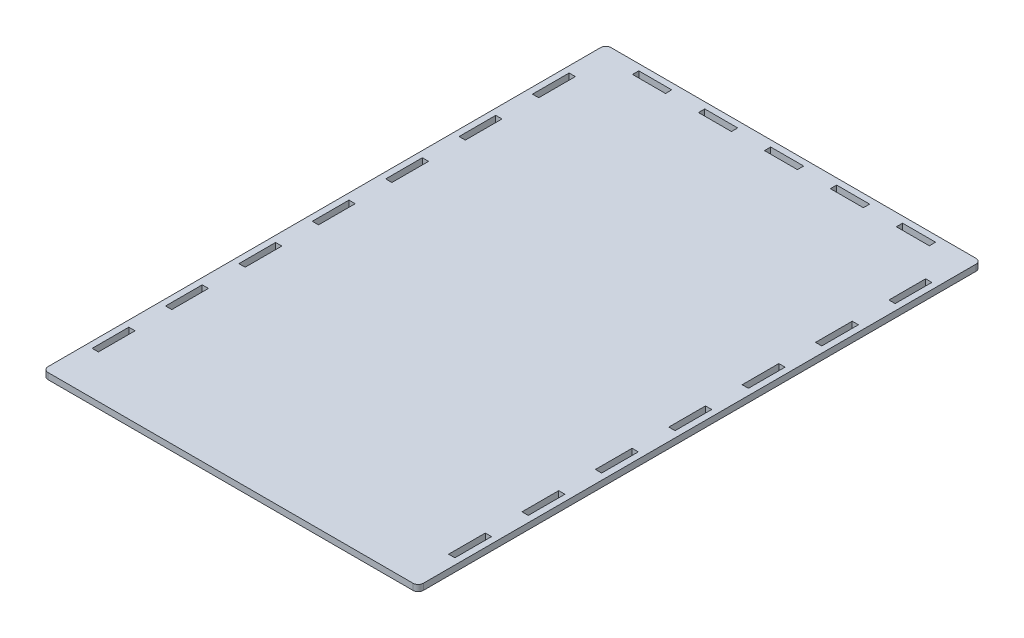
SolidWorks part; units mm, degrees
ref_plane "Front Plane" through (0, 0, 0) normal (0, 0, 1) x (1, 0, 0)
ref_plane "Top Plane" through (0, 0, 0) normal (0, 1, 0) x (1, 0, 0)
ref_plane "Right Plane" through (0, 0, 0) normal (1, 0, 0) x (0, 0, -1)
sketch "Sketch1" plane through (0, 0, 0) normal (0, 1, 0) x (1, 0, 0)
  line L3 (90, 135) -> (90, -135)
  line L6 (90, -135) -> (-90, -135)
  line L9 (-90, -135) -> (-90, 135)
  line L14 (-90, 135) -> (90, 135)
  line L15 (0, 135) -> (0, -135) construction
  point P1 (0, 0)
  point P4 (0, 135)
  point P21 (0, -135)
  dimension "D1" = 180
  dimension "D3" = 270
extrude "Boss-Extrude1" add sketch "Sketch1" along normal blind 3
sketch "Sketch2" plane through (0, 3, 0) normal (0, 1, 0) x (1, 0, 0)
  line L0 (-55.3636, 129) -> (-39.5455, 129) construction
  line L1 (-7.9091, 129) -> (7.9091, 129)
  line L2 (-7.9091, 129) -> (-7.9091, 132)
  line L3 (-7.9091, 132) -> (7.9091, 132)
  line L4 (7.9091, 129) -> (7.9091, 132)
  line L5 (-7.9091, 129) -> (7.9091, 132) construction
  line L6 (-7.9091, 132) -> (7.9091, 129) construction
  line L7 (23.7273, 129) -> (39.5455, 129)
  line L8 (23.7273, 129) -> (23.7273, 132)
  line L9 (23.7273, 132) -> (39.5455, 132)
  line L10 (39.5455, 129) -> (39.5455, 132)
  line L11 (23.7273, 129) -> (39.5455, 132) construction
  line L12 (23.7273, 132) -> (39.5455, 129) construction
  line L13 (55.3636, 129) -> (71.1818, 129)
  line L14 (55.3636, 129) -> (55.3636, 132)
  line L15 (55.3636, 132) -> (71.1818, 132)
  line L16 (87, 132) -> (-87, 132)
  line L17 (-87, 132) -> (-87, -132)
  line L18 (-90, 135) -> (-90, -135) construction
  line L19 (84, -79.2) -> (84, -96.8) construction
  line L20 (-87, -132) -> (87, -132)
  line L21 (87, -79.2) -> (84, -79.2)
  line L22 (87, -79.2) -> (87, -61.6)
  line L23 (87, -132) -> (87, 132)
  line L24 (87, 132) -> (-87, 132) construction
  line L32 (71.1818, 129) -> (71.1818, 132)
  line L33 (55.3636, 129) -> (71.1818, 132) construction
  line L34 (55.3636, 132) -> (71.1818, 129) construction
  line L35 (-39.5455, 129) -> (-23.7273, 129)
  line L36 (-39.5455, 129) -> (-39.5455, 132)
  line L37 (-39.5455, 132) -> (-23.7273, 132)
  line L38 (-23.7273, 129) -> (-23.7273, 132)
  line L39 (-39.5455, 129) -> (-23.7273, 132) construction
  line L40 (-39.5455, 132) -> (-23.7273, 129) construction
  line L41 (-71.1818, 129) -> (-55.3636, 129)
  line L42 (-71.1818, 129) -> (-71.1818, 132)
  line L43 (-71.1818, 132) -> (-55.3636, 132)
  line L44 (-55.3636, 129) -> (-55.3636, 132)
  line L45 (-71.1818, 129) -> (-55.3636, 132) construction
  line L46 (-71.1818, 132) -> (-55.3636, 129) construction
  line L47 (-23.7273, 129) -> (-7.9091, 129) construction
  line L48 (7.9091, 129) -> (23.7273, 129) construction
  line L49 (39.5455, 129) -> (55.3636, 129) construction
  line L50 (71.1818, 129) -> (87, 129) construction
  line L51 (-71.1818, 129) -> (-87, 129) construction
  line L52 (87, -61.6) -> (84, -61.6)
  line L57 (84, -79.2) -> (84, -61.6)
  line L58 (87, -79.2) -> (84, -61.6) construction
  line L63 (87, -61.6) -> (84, -79.2) construction
  line L64 (87, -114.4) -> (84, -114.4)
  line L69 (87, -114.4) -> (87, -96.8)
  line L70 (87, -96.8) -> (84, -96.8)
  line L75 (84, -114.4) -> (84, -96.8)
  line L76 (87, -114.4) -> (84, -96.8) construction
  line L81 (87, -96.8) -> (84, -114.4) construction
  line L82 (84, -114.4) -> (84, -132) construction
  line L83 (-90, -135) -> (90, -135) construction
  line L84 (-84, 114.4) -> (-87, 114.4)
  line L85 (-87, 96.8) -> (-87, 114.4)
  line L86 (-84, 96.8) -> (-87, 96.8)
  line L87 (-84, 96.8) -> (-84, 114.4)
  line L88 (-84, 79.2) -> (-87, 79.2)
  line L93 (-87, 61.6) -> (-87, 79.2)
  line L94 (-84, 61.6) -> (-87, 61.6)
  line L99 (-84, 61.6) -> (-84, 79.2)
  line L100 (-84, 44) -> (-87, 44)
  line L105 (-87, 26.4) -> (-87, 44)
  line L106 (-84, 26.4) -> (-87, 26.4)
  line L107 (-84, 26.4) -> (-84, 44)
  line L108 (-84, 8.8) -> (-87, 8.8)
  line L109 (-87, -8.8) -> (-87, 8.8)
  line L110 (84, 132) -> (84, 114.4) construction
  line L111 (84, 96.8) -> (87, 96.8)
  line L112 (84, 96.8) -> (84, 114.4)
  line L113 (84, 114.4) -> (87, 114.4)
  line L114 (87, 96.8) -> (87, 114.4)
  line L115 (84, 96.8) -> (87, 114.4) construction
  line L116 (84, 114.4) -> (87, 96.8) construction
  line L117 (84, 61.6) -> (87, 61.6)
  line L118 (84, 61.6) -> (84, 79.2)
  line L119 (84, 79.2) -> (87, 79.2)
  line L120 (87, 61.6) -> (87, 79.2)
  line L121 (84, 61.6) -> (87, 79.2) construction
  line L122 (84, 79.2) -> (87, 61.6) construction
  line L123 (84, 26.4) -> (87, 26.4)
  line L124 (84, 26.4) -> (84, 44)
  line L125 (84, 44) -> (87, 44)
  line L126 (87, 26.4) -> (87, 44)
  line L127 (84, 26.4) -> (87, 44) construction
  line L128 (84, 44) -> (87, 26.4) construction
  line L129 (84, -8.8) -> (87, -8.8)
  line L130 (84, -8.8) -> (84, 8.8)
  line L131 (84, 8.8) -> (87, 8.8)
  line L132 (87, -8.8) -> (87, 8.8)
  line L133 (84, -8.8) -> (87, 8.8) construction
  line L134 (84, 8.8) -> (87, -8.8) construction
  line L135 (84, -44) -> (87, -44)
  line L136 (84, -44) -> (84, -26.4)
  line L137 (84, -26.4) -> (87, -26.4)
  line L138 (87, -44) -> (87, -26.4)
  line L139 (84, -44) -> (87, -26.4) construction
  line L140 (84, -26.4) -> (87, -44) construction
  line L141 (84, 96.8) -> (84, 79.2) construction
  line L142 (84, 61.6) -> (84, 44) construction
  line L143 (84, 26.4) -> (84, 8.8) construction
  line L144 (84, -8.8) -> (84, -26.4) construction
  line L145 (84, -44) -> (84, -61.6) construction
  line L146 (-84, -8.8) -> (-87, -8.8)
  line L151 (-84, -8.8) -> (-84, 8.8)
  line L152 (-84, -26.4) -> (-87, -26.4)
  line L153 (-87, -44) -> (-87, -26.4)
  line L154 (0, -1278.0896) -> (0, 48721.9104) construction
  line L191 (-84, -44) -> (-87, -44)
  line L192 (-84, -44) -> (-84, -26.4)
  line L193 (-87, -61.6) -> (-84, -61.6)
  line L194 (-84, -79.2) -> (-84, -61.6)
  line L195 (-87, -79.2) -> (-84, -79.2)
  line L196 (-87, -79.2) -> (-87, -61.6)
  line L197 (-87, -96.8) -> (-84, -96.8)
  line L198 (-84, -114.4) -> (-84, -96.8)
  line L199 (-87, -114.4) -> (-84, -114.4)
  line L200 (-87, -114.4) -> (-87, -96.8)
  point P0 (0, 130.5)
  point P5 (31.6364, 130.5)
  point P12 (63.2727, 130.5)
  point P18 (85.5, -105.6)
  point P21 (-31.6364, 130.5)
  point P28 (-63.2727, 130.5)
  point P39 (85.5, -70.4)
  point P78 (85.5, 70.4)
  point P82 (85.5, 105.6)
  point P89 (85.5, 35.2)
  point P94 (85.5, 0)
  point P99 (85.5, -35.2)
  dimension "D2" = 3
  dimension "D3" = 3
  dimension "D4" = 3
  dimension "D5" = 3
  dimension "D1" = 3
extrude "Cut-Extrude1" cut sketch "Sketch2" against normal through all both and the other way through all
fillet "Fillet1" radius 2.5 4 edges at (-90, 1.5, -135) (90, 1.5, -135) (90, 1.5, 135) (-90, 1.5, 135)
sketch "Sketch3" plane through (0, 0, 0) normal (0, 1, 0) x (1, 0, 0)
  line L0 (-145.7809, -27.5) -> (-165.9882, -27.5)
  line L1 (-145.7809, -72.5) -> (-165.9882, -72.5)
  line L2 (-165.9882, -72.5) -> (-176.0918, -90)
  line L3 (-176.0918, -90) -> (-165.9882, -107.5)
  line L4 (-165.9882, -107.5) -> (-145.7809, -107.5)
  line L5 (-145.7809, -107.5) -> (-135.6773, -90)
  line L6 (-135.6773, -90) -> (-145.7809, -72.5)
  line L13 (-165.9882, -27.5) -> (-176.0918, -45)
  line L14 (-137.1207, -112.5) -> (-127.0171, -130)
  line L15 (-127.0171, -130) -> (-106.8098, -130)
  line L16 (-106.8098, -130) -> (-96.7062, -112.5)
  line L17 (-96.7062, -112.5) -> (-106.8098, -95)
  line L18 (-106.8098, -95) -> (-127.0171, -95)
  line L19 (-127.0171, -95) -> (-137.1207, -112.5)
  line L20 (-176.0918, -45) -> (-165.9882, -62.5)
  line L21 (-165.9882, -62.5) -> (-145.7809, -62.5)
  line L22 (-145.7809, -62.5) -> (-135.6773, -45)
  line L23 (-135.6773, -45) -> (-145.7809, -27.5)
  line L24 (-137.1207, -67.5) -> (-127.0171, -85)
  line L25 (-127.0171, -85) -> (-106.8098, -85)
  line L26 (-106.8098, -85) -> (-96.7062, -67.5)
  line L27 (-96.7062, -67.5) -> (-106.8098, -50)
  line L28 (-106.8098, -50) -> (-127.0171, -50)
  line L29 (-127.0171, -50) -> (-137.1207, -67.5)
  line L30 (-145.7809, 17.5) -> (-165.9882, 17.5)
  line L31 (-165.9882, 17.5) -> (-176.0918, 0)
  line L32 (-176.0918, 0) -> (-165.9882, -17.5)
  line L33 (-165.9882, -17.5) -> (-145.7809, -17.5)
  line L34 (-145.7809, -17.5) -> (-135.6773, 0)
  line L35 (-135.6773, 0) -> (-145.7809, 17.5)
  line L36 (-137.1207, -22.5) -> (-127.0171, -40)
  line L37 (-127.0171, -40) -> (-106.8098, -40)
  line L38 (-106.8098, -40) -> (-96.7062, -22.5)
  line L39 (-96.7062, -22.5) -> (-106.8098, -5)
  line L40 (-106.8098, -5) -> (-127.0171, -5)
  line L41 (-127.0171, -5) -> (-137.1207, -22.5)
  line L42 (-145.7809, 62.5) -> (-165.9882, 62.5)
  line L43 (-165.9882, 62.5) -> (-176.0918, 45)
  line L44 (-176.0918, 45) -> (-165.9882, 27.5)
  line L45 (-165.9882, 27.5) -> (-145.7809, 27.5)
  line L46 (-145.7809, 27.5) -> (-135.6773, 45)
  line L47 (-135.6773, 45) -> (-145.7809, 62.5)
  line L48 (-137.1207, 22.5) -> (-127.0171, 5)
  line L49 (-127.0171, 5) -> (-106.8098, 5)
  line L50 (-106.8098, 5) -> (-96.7062, 22.5)
  line L51 (-96.7062, 22.5) -> (-106.8098, 40)
  line L52 (-106.8098, 40) -> (-127.0171, 40)
  line L53 (-127.0171, 40) -> (-137.1207, 22.5)
  line L54 (-145.7809, 107.5) -> (-165.9882, 107.5)
  line L55 (-165.9882, 107.5) -> (-176.0918, 90)
  line L56 (-176.0918, 90) -> (-165.9882, 72.5)
  line L57 (-165.9882, 72.5) -> (-145.7809, 72.5)
  line L58 (-145.7809, 72.5) -> (-135.6773, 90)
  line L59 (-135.6773, 90) -> (-145.7809, 107.5)
  line L60 (-137.1207, 67.5) -> (-127.0171, 50)
  line L61 (-127.0171, 50) -> (-106.8098, 50)
  line L62 (-106.8098, 50) -> (-96.7062, 67.5)
  line L63 (-96.7062, 67.5) -> (-106.8098, 85)
  line L64 (-106.8098, 85) -> (-127.0171, 85)
  line L65 (-127.0171, 85) -> (-137.1207, 67.5)
  line L66 (-145.7809, 152.5) -> (-165.9882, 152.5)
  line L67 (-165.9882, 152.5) -> (-176.0918, 135)
  line L68 (-176.0918, 135) -> (-165.9882, 117.5)
  line L69 (-165.9882, 117.5) -> (-145.7809, 117.5)
  line L70 (-145.7809, 117.5) -> (-135.6773, 135)
  line L71 (-135.6773, 135) -> (-145.7809, 152.5)
  line L72 (-137.1207, 112.5) -> (-127.0171, 95)
  line L73 (-127.0171, 95) -> (-106.8098, 95)
  line L74 (-106.8098, 95) -> (-96.7062, 112.5)
  line L75 (-96.7062, 112.5) -> (-106.8098, 130)
  line L76 (-106.8098, 130) -> (-127.0171, 130)
  line L77 (-127.0171, 130) -> (-137.1207, 112.5)
  line L102 (-145.7809, -72.5) -> (-145.7809, -27.5) construction
  line L103 (-127.0171, -95) -> (-127.0171, -85) construction
  line L104 (-140.7291, -81.25) -> (-132.0689, -76.25) construction
  line L105 (-59.1784, 112.5) -> (-49.0748, 95)
  line L106 (-49.0748, 95) -> (-28.8675, 95)
  line L107 (-28.8675, 95) -> (-18.7639, 112.5)
  line L108 (-18.7639, 112.5) -> (-28.8675, 130)
  line L109 (-28.8675, 130) -> (-49.0748, 130)
  line L110 (-49.0748, 130) -> (-59.1784, 112.5)
  line L111 (-67.8387, 152.5) -> (-88.0459, 152.5)
  line L112 (-88.0459, 152.5) -> (-98.1495, 135)
  line L113 (-98.1495, 135) -> (-88.0459, 117.5)
  line L114 (-88.0459, 117.5) -> (-67.8387, 117.5)
  line L115 (-67.8387, 117.5) -> (-57.735, 135)
  line L116 (-57.735, 135) -> (-67.8387, 152.5)
  line L117 (-67.8387, 107.5) -> (-88.0459, 107.5)
  line L118 (-88.0459, 107.5) -> (-98.1495, 90)
  line L119 (-98.1495, 90) -> (-88.0459, 72.5)
  line L120 (-88.0459, 72.5) -> (-67.8387, 72.5)
  line L121 (-67.8387, 72.5) -> (-57.735, 90)
  line L122 (-57.735, 90) -> (-67.8387, 107.5)
  line L123 (-67.8387, 62.5) -> (-88.0459, 62.5)
  line L124 (-88.0459, 62.5) -> (-98.1495, 45)
  line L125 (-98.1495, 45) -> (-88.0459, 27.5)
  line L126 (-88.0459, 27.5) -> (-67.8387, 27.5)
  line L127 (-67.8387, 27.5) -> (-57.735, 45)
  line L128 (-57.735, 45) -> (-67.8387, 62.5)
  line L129 (-67.8387, 17.5) -> (-88.0459, 17.5)
  line L130 (-88.0459, 17.5) -> (-98.1495, 0)
  line L131 (-98.1495, 0) -> (-88.0459, -17.5)
  line L132 (-88.0459, -17.5) -> (-67.8387, -17.5)
  line L133 (-67.8387, -17.5) -> (-57.735, 0)
  line L134 (-57.735, 0) -> (-67.8387, 17.5)
  line L135 (-59.1784, -22.5) -> (-49.0748, -40)
  line L136 (-49.0748, -40) -> (-28.8675, -40)
  line L137 (-28.8675, -40) -> (-18.7639, -22.5)
  line L138 (-18.7639, -22.5) -> (-28.8675, -5)
  line L139 (-28.8675, -5) -> (-49.0748, -5)
  line L140 (-49.0748, -5) -> (-59.1784, -22.5)
  line L141 (-67.8387, -27.5) -> (-88.0459, -27.5)
  line L142 (-88.0459, -27.5) -> (-98.1495, -45)
  line L143 (-98.1495, -45) -> (-88.0459, -62.5)
  line L144 (-88.0459, -62.5) -> (-67.8387, -62.5)
  line L145 (-67.8387, -62.5) -> (-57.735, -45)
  line L146 (-57.735, -45) -> (-67.8387, -27.5)
  line L147 (-59.1784, -67.5) -> (-49.0748, -85)
  line L148 (-49.0748, -85) -> (-28.8675, -85)
  line L149 (-28.8675, -85) -> (-18.7639, -67.5)
  line L150 (-18.7639, -67.5) -> (-28.8675, -50)
  line L151 (-28.8675, -50) -> (-49.0748, -50)
  line L152 (-49.0748, -50) -> (-59.1784, -67.5)
  line L153 (-67.8387, -72.5) -> (-88.0459, -72.5)
  line L154 (-88.0459, -72.5) -> (-98.1495, -90)
  line L155 (-98.1495, -90) -> (-88.0459, -107.5)
  line L156 (-88.0459, -107.5) -> (-67.8387, -107.5)
  line L157 (-67.8387, -107.5) -> (-57.735, -90)
  line L158 (-57.735, -90) -> (-67.8387, -72.5)
  line L159 (-59.1784, -112.5) -> (-49.0748, -130)
  line L160 (-49.0748, -130) -> (-28.8675, -130)
  line L161 (-28.8675, -130) -> (-18.7639, -112.5)
  line L162 (-18.7639, -112.5) -> (-28.8675, -95)
  line L163 (-28.8675, -95) -> (-49.0748, -95)
  line L164 (-49.0748, -95) -> (-59.1784, -112.5)
  line L165 (-59.1784, 22.5) -> (-49.0748, 5)
  line L166 (-49.0748, 5) -> (-28.8675, 5)
  line L167 (-28.8675, 5) -> (-18.7639, 22.5)
  line L168 (-18.7639, 22.5) -> (-28.8675, 40)
  line L169 (-28.8675, 40) -> (-49.0748, 40)
  line L170 (-49.0748, 40) -> (-59.1784, 22.5)
  line L171 (-59.1784, 67.5) -> (-49.0748, 50)
  line L172 (-49.0748, 50) -> (-28.8675, 50)
  line L173 (-28.8675, 50) -> (-18.7639, 67.5)
  line L174 (-18.7639, 67.5) -> (-28.8675, 85)
  line L175 (-28.8675, 85) -> (-49.0748, 85)
  line L176 (-49.0748, 85) -> (-59.1784, 67.5)
  line L177 (18.7639, 112.5) -> (28.8675, 95)
  line L178 (28.8675, 95) -> (49.0748, 95)
  line L179 (49.0748, 95) -> (59.1784, 112.5)
  line L180 (59.1784, 112.5) -> (49.0748, 130)
  line L181 (49.0748, 130) -> (28.8675, 130)
  line L182 (28.8675, 130) -> (18.7639, 112.5)
  line L183 (10.1036, 152.5) -> (-10.1036, 152.5)
  line L184 (-10.1036, 152.5) -> (-20.2073, 135)
  line L185 (-20.2073, 135) -> (-10.1036, 117.5)
  line L186 (-10.1036, 117.5) -> (10.1036, 117.5)
  line L187 (10.1036, 117.5) -> (20.2073, 135)
  line L188 (20.2073, 135) -> (10.1036, 152.5)
  line L189 (10.1036, 107.5) -> (-10.1036, 107.5)
  line L190 (-10.1036, 107.5) -> (-20.2073, 90)
  line L191 (-20.2073, 90) -> (-10.1036, 72.5)
  line L192 (-10.1036, 72.5) -> (10.1036, 72.5)
  line L193 (10.1036, 72.5) -> (20.2073, 90)
  line L194 (20.2073, 90) -> (10.1036, 107.5)
  line L195 (10.1036, 62.5) -> (-10.1036, 62.5)
  line L196 (-10.1036, 62.5) -> (-20.2073, 45)
  line L197 (-20.2073, 45) -> (-10.1036, 27.5)
  line L198 (-10.1036, 27.5) -> (10.1036, 27.5)
  line L199 (10.1036, 27.5) -> (20.2073, 45)
  line L200 (20.2073, 45) -> (10.1036, 62.5)
  line L201 (10.1036, 17.5) -> (-10.1036, 17.5)
  line L202 (-10.1036, 17.5) -> (-20.2073, 0)
  line L203 (-20.2073, 0) -> (-10.1036, -17.5)
  line L204 (-10.1036, -17.5) -> (10.1036, -17.5)
  line L205 (10.1036, -17.5) -> (20.2073, 0)
  line L206 (20.2073, 0) -> (10.1036, 17.5)
  line L207 (18.7639, -22.5) -> (28.8675, -40)
  line L208 (28.8675, -40) -> (49.0748, -40)
  line L209 (49.0748, -40) -> (59.1784, -22.5)
  line L210 (59.1784, -22.5) -> (49.0748, -5)
  line L211 (49.0748, -5) -> (28.8675, -5)
  line L212 (28.8675, -5) -> (18.7639, -22.5)
  line L213 (10.1036, -27.5) -> (-10.1036, -27.5)
  line L214 (-10.1036, -27.5) -> (-20.2073, -45)
  line L215 (-20.2073, -45) -> (-10.1036, -62.5)
  line L216 (-10.1036, -62.5) -> (10.1036, -62.5)
  line L217 (10.1036, -62.5) -> (20.2073, -45)
  line L218 (20.2073, -45) -> (10.1036, -27.5)
  line L219 (18.7639, -67.5) -> (28.8675, -85)
  line L220 (28.8675, -85) -> (49.0748, -85)
  line L221 (49.0748, -85) -> (59.1784, -67.5)
  line L222 (59.1784, -67.5) -> (49.0748, -50)
  line L223 (49.0748, -50) -> (28.8675, -50)
  line L224 (28.8675, -50) -> (18.7639, -67.5)
  line L225 (10.1036, -72.5) -> (-10.1036, -72.5)
  line L226 (-10.1036, -72.5) -> (-20.2073, -90)
  line L227 (-20.2073, -90) -> (-10.1036, -107.5)
  line L228 (-10.1036, -107.5) -> (10.1036, -107.5)
  line L229 (10.1036, -107.5) -> (20.2073, -90)
  line L230 (20.2073, -90) -> (10.1036, -72.5)
  line L231 (18.7639, -112.5) -> (28.8675, -130)
  line L232 (28.8675, -130) -> (49.0748, -130)
  line L233 (49.0748, -130) -> (59.1784, -112.5)
  line L234 (59.1784, -112.5) -> (49.0748, -95)
  line L235 (49.0748, -95) -> (28.8675, -95)
  line L236 (28.8675, -95) -> (18.7639, -112.5)
  line L237 (18.7639, 22.5) -> (28.8675, 5)
  line L238 (28.8675, 5) -> (49.0748, 5)
  line L239 (49.0748, 5) -> (59.1784, 22.5)
  line L240 (59.1784, 22.5) -> (49.0748, 40)
  line L241 (49.0748, 40) -> (28.8675, 40)
  line L242 (28.8675, 40) -> (18.7639, 22.5)
  line L243 (18.7639, 67.5) -> (28.8675, 50)
  line L244 (28.8675, 50) -> (49.0748, 50)
  line L245 (49.0748, 50) -> (59.1784, 67.5)
  line L246 (59.1784, 67.5) -> (49.0748, 85)
  line L247 (49.0748, 85) -> (28.8675, 85)
  line L248 (28.8675, 85) -> (18.7639, 67.5)
  line L249 (96.7062, 112.5) -> (106.8098, 95)
  line L250 (106.8098, 95) -> (127.0171, 95)
  line L251 (127.0171, 95) -> (137.1207, 112.5)
  line L252 (137.1207, 112.5) -> (127.0171, 130)
  line L253 (127.0171, 130) -> (106.8098, 130)
  line L254 (106.8098, 130) -> (96.7062, 112.5)
  line L255 (88.0459, 152.5) -> (67.8387, 152.5)
  line L256 (67.8387, 152.5) -> (57.735, 135)
  line L257 (57.735, 135) -> (67.8387, 117.5)
  line L258 (67.8387, 117.5) -> (88.0459, 117.5)
  line L259 (88.0459, 117.5) -> (98.1495, 135)
  line L260 (98.1495, 135) -> (88.0459, 152.5)
  line L261 (88.0459, 107.5) -> (67.8387, 107.5)
  line L262 (67.8387, 107.5) -> (57.735, 90)
  line L263 (57.735, 90) -> (67.8387, 72.5)
  line L264 (67.8387, 72.5) -> (88.0459, 72.5)
  line L265 (88.0459, 72.5) -> (98.1495, 90)
  line L266 (98.1495, 90) -> (88.0459, 107.5)
  line L267 (88.0459, 62.5) -> (67.8387, 62.5)
  line L268 (67.8387, 62.5) -> (57.735, 45)
  line L269 (57.735, 45) -> (67.8387, 27.5)
  line L270 (67.8387, 27.5) -> (88.0459, 27.5)
  line L271 (88.0459, 27.5) -> (98.1495, 45)
  line L272 (98.1495, 45) -> (88.0459, 62.5)
  line L273 (88.0459, 17.5) -> (67.8387, 17.5)
  line L274 (67.8387, 17.5) -> (57.735, 0)
  line L275 (57.735, 0) -> (67.8387, -17.5)
  line L276 (67.8387, -17.5) -> (88.0459, -17.5)
  line L277 (88.0459, -17.5) -> (98.1495, 0)
  line L278 (98.1495, 0) -> (88.0459, 17.5)
  line L279 (96.7062, -22.5) -> (106.8098, -40)
  line L280 (106.8098, -40) -> (127.0171, -40)
  line L281 (127.0171, -40) -> (137.1207, -22.5)
  line L282 (137.1207, -22.5) -> (127.0171, -5)
  line L283 (127.0171, -5) -> (106.8098, -5)
  line L284 (106.8098, -5) -> (96.7062, -22.5)
  line L285 (88.0459, -27.5) -> (67.8387, -27.5)
  line L286 (67.8387, -27.5) -> (57.735, -45)
  line L287 (57.735, -45) -> (67.8387, -62.5)
  line L288 (67.8387, -62.5) -> (88.0459, -62.5)
  line L289 (88.0459, -62.5) -> (98.1495, -45)
  line L290 (98.1495, -45) -> (88.0459, -27.5)
  line L291 (96.7062, -67.5) -> (106.8098, -85)
  line L292 (106.8098, -85) -> (127.0171, -85)
  line L293 (127.0171, -85) -> (137.1207, -67.5)
  line L294 (137.1207, -67.5) -> (127.0171, -50)
  line L295 (127.0171, -50) -> (106.8098, -50)
  line L296 (106.8098, -50) -> (96.7062, -67.5)
  line L297 (88.0459, -72.5) -> (67.8387, -72.5)
  line L298 (67.8387, -72.5) -> (57.735, -90)
  line L299 (57.735, -90) -> (67.8387, -107.5)
  line L300 (67.8387, -107.5) -> (88.0459, -107.5)
  line L301 (88.0459, -107.5) -> (98.1495, -90)
  line L302 (98.1495, -90) -> (88.0459, -72.5)
  line L303 (96.7062, -112.5) -> (106.8098, -130)
  line L304 (106.8098, -130) -> (127.0171, -130)
  line L305 (127.0171, -130) -> (137.1207, -112.5)
  line L306 (137.1207, -112.5) -> (127.0171, -95)
  line L307 (127.0171, -95) -> (106.8098, -95)
  line L308 (106.8098, -95) -> (96.7062, -112.5)
  line L309 (96.7062, 22.5) -> (106.8098, 5)
  line L310 (106.8098, 5) -> (127.0171, 5)
  line L311 (127.0171, 5) -> (137.1207, 22.5)
  line L312 (137.1207, 22.5) -> (127.0171, 40)
  line L313 (127.0171, 40) -> (106.8098, 40)
  line L314 (106.8098, 40) -> (96.7062, 22.5)
  line L315 (96.7062, 67.5) -> (106.8098, 50)
  line L316 (106.8098, 50) -> (127.0171, 50)
  line L317 (127.0171, 50) -> (137.1207, 67.5)
  line L318 (137.1207, 67.5) -> (127.0171, 85)
  line L319 (127.0171, 85) -> (106.8098, 85)
  line L320 (106.8098, 85) -> (96.7062, 67.5)
  line L321 (-137.1207, 112.5) -> (-59.1784, 112.5) construction
  line L322 (-93.0977, -81.25) -> (-101.758, -76.25) construction
  line L323 (84, 96.8) -> (84, 114.4) construction
  line L328 (-72, -117) -> (72, -117)
  line L329 (-72, -117) -> (-72, 117)
  line L330 (-72, 117) -> (72, 117)
  line L331 (72, -117) -> (72, 117)
  line L332 (-72, -117) -> (72, 117) construction
  line L333 (-72, 117) -> (72, -117) construction
  line L334 (71.1818, 129) -> (55.3636, 129) construction
  circle A0 centre (-155.8846, -90) radius 17.5 construction
  circle A1 centre (-116.9134, -112.5) radius 17.5 construction
  point P10 (-127.0171, -90)
  point P301 (0, -62.5)
  point P302 (0, 0)
  point P311 (72, 0)
  dimension "D3" = 35
  dimension "D2" = 45
  dimension "D5" = 12
  dimension "D6" = 12
  dimension "D1" = 6
  dimension "D4" = 4
extrude "Cut-Extrude3" [suppressed] cut sketch "Sketch3" against normal through all both and the other way through all contours L329 L156 L157 L158 L153 | L159 L328 L161 L162 L163 L164 | L151 L152 L147 L148 L149 L150 | L229 L230 L225 L226 L227 L228 | L231 L328 L233 L234 L235 L236 | L223 L224 L219 L220 L221 L222 | L300 L331 L297 L298 L299 | L288 L331 L285 L286 L287 | L211 L212 L207 L208 L209 L210 | L217 L218 L213 L214 L215 L216 | L139 L140 L135 L136 L137 L138 | L329 L144 L145 L146 L141 | L329 L132 L133 L134 L129 | L169 L170 L165 L166 L167 L168 | L205 L206 L201 L202 L203 L204 | L241 L242 L237 L238 L239 L240 | L276 L331 L273 L274 L275 | L270 L331 L267 L268 L269 | L247 L248 L243 L244 L245 L246 | L199 L200 L195 L196 L197 L198 | L264 L331 L261 L262 L263 | L330 L182 L177 L178 L179 L180 | L193 L194 L189 L190 L191 L192 | L330 L110 L105 L106 L107 L108 | L175 L176 L171 L172 L173 L174 | L329 L120 L121 L122 L117 | L329 L126 L127 L128 L123
equation "\"bottomLength\"= 270mm"
equation "\"topLength\"= 380mm"
equation "\"frontHeight\"= 100mm"
equation "\"height\"= 180mm"
equation "\"width\"= 180mm"
equation "\"D3@Sketch1\"=\"bottomLength\""
equation "\"D1@Sketch1\"=\"width\""
